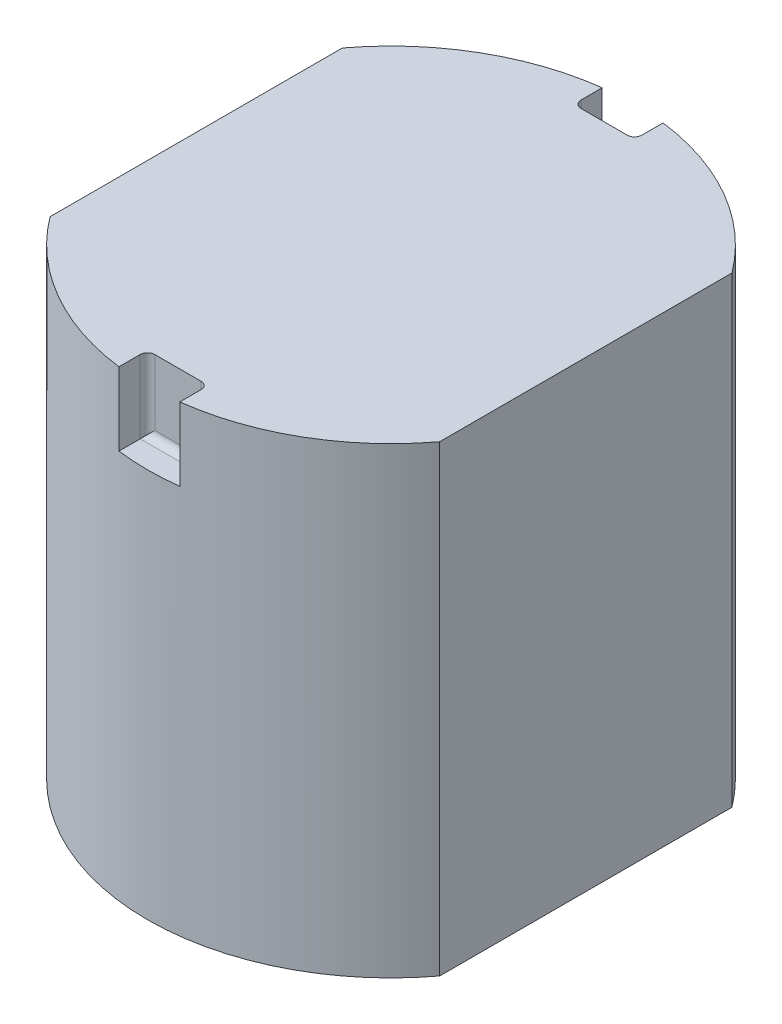
SolidWorks part; units mm, degrees
ref_plane "Front Plane" through (0, 0, 0) normal (0, 0, 1) x (1, 0, 0)
ref_plane "Top Plane" through (0, 0, 0) normal (0, 1, 0) x (1, 0, 0)
ref_plane "Right Plane" through (0, 0, 0) normal (1, 0, 0) x (0, 0, -1)
sketch "Sketch1" plane through (0, 0, 0) normal (0, 1, 0) x (1, 0, 0)
  line L2 (8, -6) -> (8, 6)
  line L4 (-8, -6) -> (-8, 6)
  line L5 (8, -6) -> (-8, 6) construction
  line L6 (8, 6) -> (-8, -6) construction
  arc A0 (-8, -6) -> (8, -6) centre (0, 0) ccw
  arc A1 (8, 6) -> (-8, 6) centre (0, 0) ccw
  dimension "D1" = 20
  dimension "D2" = 16
extrude "Boss-Extrude1" add sketch "Sketch1" along normal blind 19
sketch "Sketch2" plane through (0, 19, 0) normal (0, 1, 0) x (1, 0, 0)
  line L0 (-8, -6) -> (8, -6) construction
  line L2 (-1.25, -8.75) -> (1.25, -8.75)
  line L3 (-1.25, -8.75) -> (-1.25, -11.25)
  line L4 (-1.25, -11.25) -> (1.25, -11.25)
  line L5 (1.25, -8.75) -> (1.25, -11.25)
  line L6 (-1.25, -8.75) -> (1.25, -11.25) construction
  line L7 (-1.25, -11.25) -> (1.25, -8.75) construction
  arc A0 (-8, -6) -> (8, -6) centre (0, 0) ccw construction
  point P4 (0, -10)
  dimension "D1" = 2.5
  dimension "D2" = 2.5
extrude "Cut-Extrude1" cut sketch "Sketch2" against normal blind 3
mirror "Mirror1" about plane through (0, 0, 0) normal (0, 0, 1) of "Cut-Extrude1"
fillet "Fillet1" radius 0.3 6 edges at (0, 16, -8.75) (0, 16, 8.75) (1.25, 17.5, -8.75) (-1.25, 17.5, -8.75) (1.25, 17.5, 8.75) (-1.25, 17.5, 8.75)
